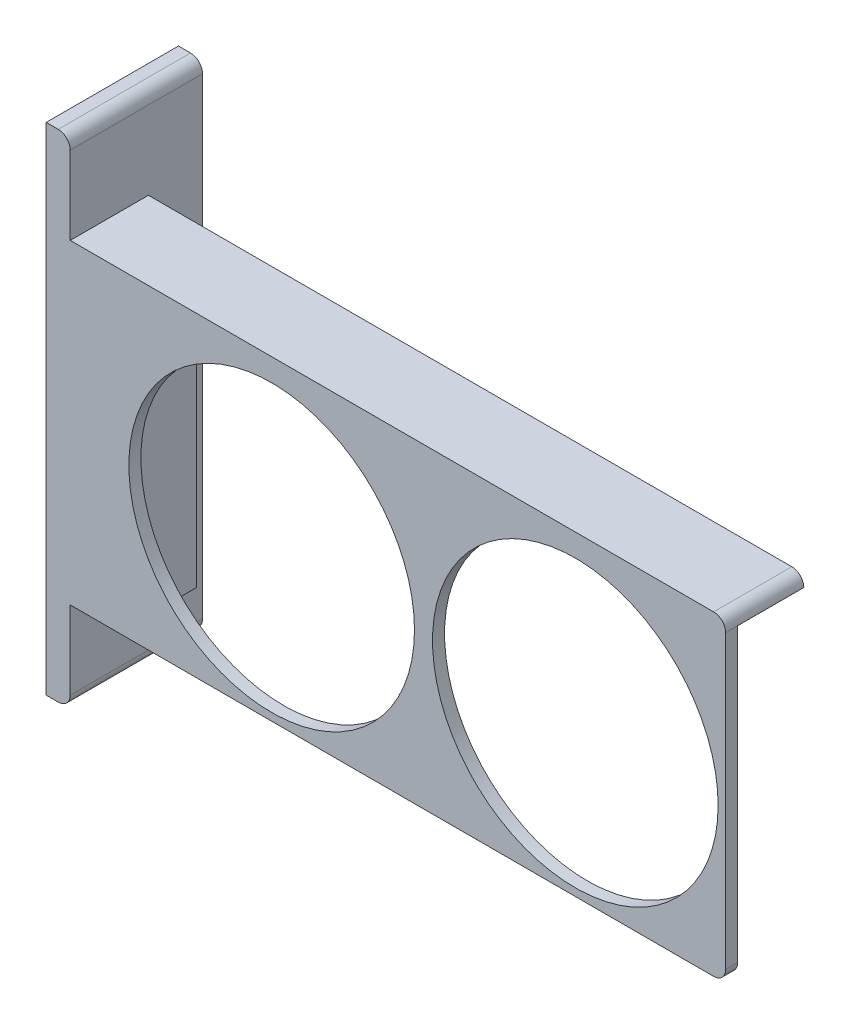
SolidWorks part; units mm, degrees
ref_plane "정면" through (0, 0, 0) normal (0, 0, 1) x (1, 0, 0)
ref_plane "윗면" through (0, 0, 0) normal (0, 1, 0) x (1, 0, 0)
ref_plane "우측면" through (0, 0, 0) normal (1, 0, 0) x (0, 0, -1)
sketch "스케치1" plane through (0, 0, 0) normal (0, 0, 1) x (1, 0, 0)
  line L1 (0, 0) -> (113, 0)
  line L2 (0, 0) -> (0, 52.5)
  line L3 (0, 52.5) -> (113, 52.5)
  line L4 (113, 0) -> (113, 52.5)
  circle A0 centre (88, 25) radius 23.75
  circle A1 centre (37.5, 25) radius 23.75
  dimension "D3" = 47.5
  dimension "D4" = 47.5
  dimension "D1" = 113
  dimension "D2" = 52.5
  dimension "D5" = 25
  dimension "D6" = 25
  dimension "D7" = 25
  dimension "D8" = 50.5
extrude "보스-돌출1" add sketch "스케치1" along normal blind 2
sketch "스케치2" plane through (0, 0, 0) normal (0, 0, -1) x (-1, 0, 0)
  line L0 (0, 52.5) -> (0, 0) construction
  line L1 (-113, 52.5) -> (0, 52.5)
  line L2 (-113, 52.5) -> (-113, 50.5)
  line L3 (-113, 50.5) -> (0, 50.5)
  line L4 (0, 52.5) -> (0, 50.5)
  dimension "D1" = 2
extrude "보스-돌출2" add sketch "스케치2" along normal blind 11
fillet "필렛1" radius 2 2 edges at (113, 0, 1) (113, 52.5, -4.5)
sketch "스케치3" plane through (0, 0, 0) normal (0, 0, -1) x (-1, 0, 0)
  line L0 (0, 52.5) -> (-111, 52.5) construction
  line L1 (0, 0) -> (-4, 0)
  line L2 (0, 0) -> (0, 52.5)
  line L3 (0, 52.5) -> (-4, 52.5)
  line L4 (-4, 0) -> (-4, 52.5)
  dimension "D1" = 4
extrude "보스-돌출3" add sketch "스케치3" along normal blind 20
sketch "스케치4" plane through (0, 0, 0) normal (0, 0, -1) x (-1, 0, 0)
  line L0 (-37.5, 25) -> (-12, 25)
  line L1 (-4, 0) -> (-111, 0) construction
  line L2 (-4, 50.5) -> (-12, 50.5)
  line L3 (-4, 50.5) -> (-4, 0)
  line L4 (-4, 0) -> (-12, 0)
  line L5 (-12, 50.5) -> (-12, 0)
  line M3 (-111, 0) -> (-4, 0)
  line M4 (-4, 0) -> (-4, 50.5)
  line M5 (-4, 50.5) -> (-113, 50.5)
extrude "보스-돌출4" add sketch "스케치4" along normal blind 11 contours L5 M5 M3 M4
sketch "스케치5" plane through (0, 52.5, 0) normal (0, 1, 0) x (1, 0, 0)
  line L0 (111, -2) -> (0, -2) construction
  line L1 (0, 20) -> (4, 20)
  line L2 (0, 20) -> (0, -2)
  line L3 (0, -2) -> (4, -2)
  line L4 (4, 20) -> (4, -2)
extrude "보스-돌출5" add sketch "스케치5" along normal blind 15 and the other way blind 67.5
fillet "필렛2" radius 2 2 edges at (4, 67.5, -9) (4, -15, -9)
